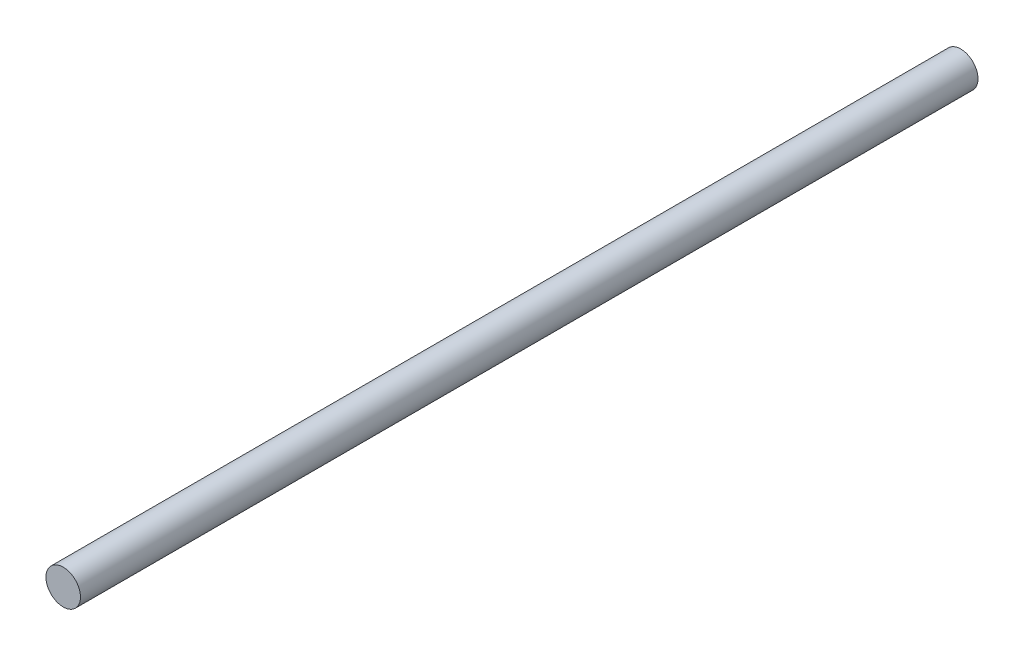
SolidWorks part; units mm, degrees
ref_plane "Front Plane" through (0, 0, 0) normal (0, 0, 1) x (1, 0, 0)
ref_plane "Top Plane" through (0, 0, 0) normal (0, 1, 0) x (1, 0, 0)
ref_plane "Right Plane" through (0, 0, 0) normal (1, 0, 0) x (0, 0, -1)
sketch "Sketch1" plane through (0, 0, 0) normal (0, 0, 1) x (1, 0, 0)
  circle A0 centre (0, 0) radius 6.35
  dimension "D1" = 12.7
extrude "Boss-Extrude1" add sketch "Sketch1" along normal blind 330.2
